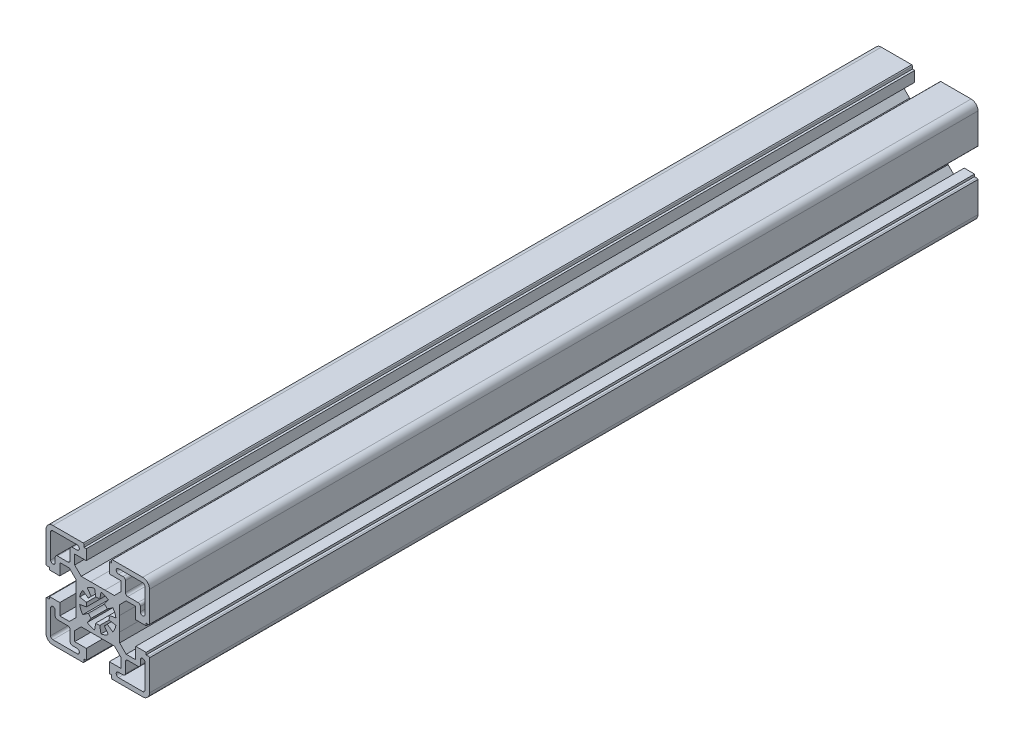
SolidWorks part; units mm, degrees
material "7050-T73510"
ref_plane "Front Plane" through (0, 0, 0) normal (0, 0, 1) x (1, 0, 0)
ref_plane "Top Plane" through (0, 0, 0) normal (0, 1, 0) x (1, 0, 0)
ref_plane "Right Plane" through (0, 0, 0) normal (1, 0, 0) x (0, 0, -1)
sketch "Sketch1" plane through (0, 0, 0) normal (0, 0, 1) x (1, 0, 0)
  line L0 (0, 34.901) -> (0, -38.8683) construction
  line L1 (-27.7848, -31.1091) -> (42.6814, -31.1091) construction
  line L3 (-0.8682, 4.924) -> (-1.3892, 7.8785)
  line L4 (-4.5886, 6.5532) -> (-2.8679, 4.0957)
  line L5 (-4.0957, 2.8679) -> (-6.5532, 4.5886)
  line L6 (-7.8784, 1.3892) -> (-4.924, 0.8682)
  line L10 (4.924, 0.8682) -> (7.8785, 1.3892)
  line L12 (6.5532, 4.5886) -> (4.0957, 2.8679)
  line L30 (-9.5, 3.1227) -> (-9.5, 7.207)
  line L31 (-9.5, 7.207) -> (-12.3429, 10.0499)
  line L32 (-12.3429, 10.0499) -> (-16.5, 10.0499)
  line L33 (-16.5, 10.0499) -> (-16.5, 4.9999)
  line L34 (-16.5, 4.9999) -> (-20.9999, 4.9999)
  line L35 (-20.9999, 4.9999) -> (-20.9999, 6)
  line L36 (-20.9999, 6) -> (-21.9999, 6)
  line L37 (-22.4999, 6.2999) -> (-22.4999, 19.5)
  line L38 (-19.4999, 22.5) -> (-6.3, 22.5)
  line L39 (-6, 21.9999) -> (-6, 20.9999)
  line L40 (-6, 20.9999) -> (-5, 20.9999)
  line L41 (-5, 20.9999) -> (-5, 16.5)
  line L42 (-5, 16.5) -> (-10.0501, 16.5)
  line L43 (-10.0501, 16.5) -> (-10.0501, 12.3428)
  line L44 (-10.0501, 12.3428) -> (-7.2071, 9.4999)
  line L45 (-7.2071, 9.4999) -> (-3.1228, 9.4999)
  line L82 (2.8679, 4.0957) -> (4.5886, 6.5532)
  line L83 (1.3892, 7.8784) -> (0.8682, 4.924)
  line L85 (3.1227, 9.5) -> (7.207, 9.5)
  line L86 (7.207, 9.5) -> (10.0499, 12.3429)
  line L87 (10.0499, 12.3429) -> (10.0499, 16.5)
  line L94 (-17.5001, 12) -> (-13.0001, 12)
  line L95 (-12.0001, 13) -> (-12.0001, 17.4999)
  line L96 (-11.0001, 18.4999) -> (-9.0001, 18.4999)
  line L97 (-19.5001, 20.5) -> (-9.0001, 20.5)
  line L98 (-20.5001, 8.9999) -> (-20.5001, 19.5)
  line L99 (-18.5001, 8.9999) -> (-18.5001, 11)
  line L101 (10.0499, 16.5) -> (4.9999, 16.5)
  line L102 (4.9999, 16.5) -> (4.9999, 20.9999)
  line L103 (4.9999, 20.9999) -> (6, 20.9999)
  line L104 (6, 20.9999) -> (6, 21.9999)
  line L105 (6.2999, 22.4999) -> (19.5, 22.4999)
  line L110 (22.5, 19.4999) -> (22.5, 6.3)
  line L111 (21.9999, 6) -> (20.9999, 6)
  line L118 (-3.1228, 9.4999) -> (3.1227, 9.5)
  line L119 (20.9999, 6) -> (20.9999, 5)
  line L124 (20.9999, 5) -> (16.5, 5)
  line L125 (16.5, 5) -> (16.5, 10.0501)
  line L126 (16.5, 10.0501) -> (12.3428, 10.0501)
  line L127 (12.3428, 10.0501) -> (9.4999, 7.2071)
  line L128 (9.4999, 7.2071) -> (9.4999, 3.1228)
  line L129 (12, 17.5001) -> (12, 13.0001)
  line L130 (13, 12.0001) -> (17.4999, 12.0001)
  line L131 (18.4999, 11.0001) -> (18.4999, 9.0001)
  line L132 (20.5, 19.5001) -> (20.5, 9.0001)
  line L133 (8.9999, 20.5001) -> (19.5, 20.5001)
  line L134 (8.9999, 18.5001) -> (11, 18.5001)
  line L135 (-9.5, 3.1227) -> (-9.4999, -3.1228)
  line L136 (9.4999, 3.1228) -> (9.5, -3.1227)
  line L137 (3.1228, -9.4999) -> (-3.1227, -9.5)
  line L138 (-0.8682, 4.924) -> (-1.3892, 7.8785)
  line L147 (0.8682, -4.924) -> (1.3892, -7.8785)
  line L148 (4.5886, -6.5532) -> (2.8679, -4.0957)
  line L149 (-4.924, -0.8682) -> (-7.8785, -1.3892)
  line L154 (4.0957, -2.8679) -> (6.5532, -4.5886)
  line L155 (7.8784, -1.3892) -> (4.924, -0.8682)
  line L157 (9.5, -3.1227) -> (9.5, -7.207)
  line L158 (9.5, -7.207) -> (12.3429, -10.0499)
  line L159 (12.3429, -10.0499) -> (16.5, -10.0499)
  line L160 (16.5, -10.0499) -> (16.5, -4.9999)
  line L161 (16.5, -4.9999) -> (20.9999, -4.9999)
  line L162 (20.9999, -4.9999) -> (20.9999, -6)
  line L163 (20.9999, -6) -> (21.9999, -6)
  line L164 (22.4999, -6.2999) -> (22.4999, -19.5)
  line L165 (19.4999, -22.5) -> (6.3, -22.5)
  line L166 (6, -21.9999) -> (6, -20.9999)
  line L167 (6, -20.9999) -> (5, -20.9999)
  line L168 (5, -20.9999) -> (5, -16.5)
  line L169 (5, -16.5) -> (10.0501, -16.5)
  line L176 (10.0501, -16.5) -> (10.0501, -12.3428)
  line L178 (4.924, 0.8682) -> (7.8785, 1.3892) [skipped]
  line L179 (6.5532, 4.5886) -> (4.0957, 2.8679) [skipped]
  line L180 (2.8679, 4.0957) -> (4.5886, 6.5532) [skipped]
  line L181 (1.3892, 7.8784) -> (0.8682, 4.924) [skipped]
  line L183 (3.1227, 9.5) -> (7.207, 9.5) [skipped]
  line L184 (7.207, 9.5) -> (10.0499, 12.3429) [skipped]
  line L185 (10.0499, 12.3429) -> (10.0499, 16.5) [skipped]
  line L186 (10.0499, 16.5) -> (4.9999, 16.5) [skipped]
  line L187 (4.9999, 16.5) -> (4.9999, 20.9999) [skipped]
  line L188 (4.9999, 20.9999) -> (6, 20.9999) [skipped]
  line L189 (6, 20.9999) -> (6, 21.9999) [skipped]
  line L190 (6.2999, 22.4999) -> (19.5, 22.4999) [skipped]
  line L191 (22.5, 19.4999) -> (22.5, 6.3) [skipped]
  line L192 (21.9999, 6) -> (20.9999, 6) [skipped]
  line L193 (20.9999, 6) -> (20.9999, 5) [skipped]
  line L194 (20.9999, 5) -> (16.5, 5) [skipped]
  line L195 (16.5, 5) -> (16.5, 10.0501) [skipped]
  line L196 (16.5, 10.0501) -> (12.3428, 10.0501) [skipped]
  line L197 (12.3428, 10.0501) -> (9.4999, 7.2071) [skipped]
  line L198 (9.4999, 7.2071) -> (9.4999, 3.1228) [skipped]
  line L199 (12, 17.5001) -> (12, 13.0001) [skipped]
  line L200 (13, 12.0001) -> (17.4999, 12.0001) [skipped]
  line L201 (18.4999, 11.0001) -> (18.4999, 9.0001) [skipped]
  line L202 (20.5, 19.5001) -> (20.5, 9.0001) [skipped]
  line L203 (8.9999, 20.5001) -> (19.5, 20.5001) [skipped]
  line L204 (8.9999, 18.5001) -> (11, 18.5001) [skipped]
  line L206 (0.8682, -4.924) -> (1.3892, -7.8785) [skipped]
  line L207 (4.5886, -6.5532) -> (2.8679, -4.0957) [skipped]
  line L208 (4.0957, -2.8679) -> (6.5532, -4.5886) [skipped]
  line L209 (7.8784, -1.3892) -> (4.924, -0.8682) [skipped]
  line L210 (9.5, -3.1227) -> (9.5, -7.207) [skipped]
  line L211 (9.5, -7.207) -> (12.3429, -10.0499) [skipped]
  line L212 (12.3429, -10.0499) -> (16.5, -10.0499) [skipped]
  line L213 (16.5, -10.0499) -> (16.5, -4.9999) [skipped]
  line L214 (16.5, -4.9999) -> (20.9999, -4.9999) [skipped]
  line L215 (20.9999, -4.9999) -> (20.9999, -6) [skipped]
  line L216 (20.9999, -6) -> (21.9999, -6) [skipped]
  line L217 (22.4999, -6.2999) -> (22.4999, -19.5) [skipped]
  line L218 (19.4999, -22.5) -> (6.3, -22.5) [skipped]
  line L219 (6, -21.9999) -> (6, -20.9999) [skipped]
  line L220 (6, -20.9999) -> (5, -20.9999) [skipped]
  line L221 (5, -20.9999) -> (5, -16.5) [skipped]
  line L222 (5, -16.5) -> (10.0501, -16.5) [skipped]
  line L223 (10.0501, -16.5) -> (10.0501, -12.3428) [skipped]
  line L224 (10.0501, -12.3428) -> (7.2071, -9.4999) [skipped]
  line L225 (7.2071, -9.4999) -> (3.1228, -9.4999) [skipped]
  line L226 (17.5001, -12) -> (13.0001, -12) [skipped]
  line L227 (12.0001, -13) -> (12.0001, -17.4999) [skipped]
  line L228 (11.0001, -18.4999) -> (9.0001, -18.4999) [skipped]
  line L229 (19.5001, -20.5) -> (9.0001, -20.5) [skipped]
  line L230 (20.5001, -8.9999) -> (20.5001, -19.5) [skipped]
  line L231 (18.5001, -8.9999) -> (18.5001, -11) [skipped]
  line L235 (-6.5532, -4.5886) -> (-4.0957, -2.8679) [skipped]
  line L236 (-2.8679, -4.0957) -> (-4.5886, -6.5532) [skipped]
  line L237 (-1.3892, -7.8784) -> (-0.8682, -4.924) [skipped]
  line L238 (-3.1227, -9.5) -> (-7.207, -9.5) [skipped]
  line L239 (-7.207, -9.5) -> (-10.0499, -12.3429) [skipped]
  line L240 (-10.0499, -12.3429) -> (-10.0499, -16.5) [skipped]
  line L241 (-10.0499, -16.5) -> (-4.9999, -16.5) [skipped]
  line L242 (-4.9999, -16.5) -> (-4.9999, -20.9999) [skipped]
  line L243 (-4.9999, -20.9999) -> (-6, -20.9999) [skipped]
  line L244 (-6, -20.9999) -> (-6, -21.9999) [skipped]
  line L245 (-6.2999, -22.4999) -> (-19.5, -22.4999) [skipped]
  line L246 (-22.5, -19.4999) -> (-22.5, -6.3) [skipped]
  line L247 (-21.9999, -6) -> (-20.9999, -6) [skipped]
  line L248 (-20.9999, -6) -> (-20.9999, -5) [skipped]
  line L249 (-20.9999, -5) -> (-16.5, -5) [skipped]
  line L250 (-16.5, -5) -> (-16.5, -10.0501) [skipped]
  line L251 (-16.5, -10.0501) -> (-12.3428, -10.0501) [skipped]
  line L252 (-12.3428, -10.0501) -> (-9.4999, -7.2071) [skipped]
  line L253 (-9.4999, -7.2071) -> (-9.4999, -3.1228) [skipped]
  line L254 (-12, -17.5001) -> (-12, -13.0001) [skipped]
  line L255 (-13, -12.0001) -> (-17.4999, -12.0001) [skipped]
  line L256 (-18.4999, -11.0001) -> (-18.4999, -9.0001) [skipped]
  line L257 (-20.5, -19.5001) -> (-20.5, -9.0001) [skipped]
  line L258 (-8.9999, -20.5001) -> (-19.5, -20.5001) [skipped]
  line L259 (-8.9999, -18.5001) -> (-11, -18.5001) [skipped]
  line L261 (10.0501, -12.3428) -> (7.2071, -9.4999)
  line L262 (7.2071, -9.4999) -> (3.1228, -9.4999)
  line L263 (17.5001, -12) -> (13.0001, -12)
  line L264 (12.0001, -13) -> (12.0001, -17.4999)
  line L265 (11.0001, -18.4999) -> (9.0001, -18.4999)
  line L266 (19.5001, -20.5) -> (9.0001, -20.5)
  line L267 (20.5001, -8.9999) -> (20.5001, -19.5)
  line L268 (18.5001, -8.9999) -> (18.5001, -11)
  line L272 (4.924, 0.8682) -> (7.8785, 1.3892)
  line L275 (-4.924, -0.8682) -> (-7.8785, -1.3892)
  line L276 (-6.5532, -4.5886) -> (-4.0957, -2.8679)
  line L277 (-2.8679, -4.0957) -> (-4.5886, -6.5532)
  line L278 (-1.3892, -7.8784) -> (-0.8682, -4.924)
  line L280 (-3.1227, -9.5) -> (-7.207, -9.5)
  line L281 (-7.207, -9.5) -> (-10.0499, -12.3429)
  line L282 (-10.0499, -12.3429) -> (-10.0499, -16.5)
  line L283 (-10.0499, -16.5) -> (-4.9999, -16.5)
  line L284 (-4.9999, -16.5) -> (-4.9999, -20.9999)
  line L285 (-4.9999, -20.9999) -> (-6, -20.9999)
  line L286 (-6, -20.9999) -> (-6, -21.9999)
  line L287 (-6.2999, -22.4999) -> (-19.5, -22.4999)
  line L288 (-22.5, -19.4999) -> (-22.5, -6.3)
  line L289 (-21.9999, -6) -> (-20.9999, -6)
  line L290 (-20.9999, -6) -> (-20.9999, -5)
  line L291 (-20.9999, -5) -> (-16.5, -5)
  line L292 (-16.5, -5) -> (-16.5, -10.0501)
  line L293 (-16.5, -10.0501) -> (-12.3428, -10.0501)
  line L294 (-12.3428, -10.0501) -> (-9.4999, -7.2071)
  line L295 (-9.4999, -7.2071) -> (-9.4999, -3.1228)
  line L296 (-12, -17.5001) -> (-12, -13.0001)
  line L297 (-13, -12.0001) -> (-17.4999, -12.0001)
  line L298 (-18.4999, -11.0001) -> (-18.4999, -9.0001)
  line L299 (-20.5, -19.5001) -> (-20.5, -9.0001)
  line L300 (-8.9999, -20.5001) -> (-19.5, -20.5001)
  line L301 (-8.9999, -18.5001) -> (-11, -18.5001)
  line L305 (0.8682, -4.924) -> (1.3892, -7.8785)
  arc A1 (-1.3892, 7.8785) -> (-4.5886, 6.5532) centre (0, 0) ccw
  arc A2 (-2.8679, 4.0957) -> (-4.0957, 2.8679) centre (0, 0) ccw
  arc A3 (-6.5532, 4.5886) -> (-7.8784, 1.3892) centre (0, 0) ccw
  arc A4 (-4.924, 0.8682) -> (-4.924, -0.8682) centre (0, 0) ccw
  arc A7 (0.8682, 4.924) -> (-0.8682, 4.924) centre (0, 0) ccw
  arc A8 (7.8785, 1.3892) -> (6.5532, 4.5886) centre (0, 0) ccw
  arc A20 (-22.4999, 6.2999) -> (-21.9999, 6) centre (-22.041, 6.4983) ccw
  arc A21 (-19.4999, 22.5) -> (-22.4999, 19.5) centre (-19.4999, 19.5) ccw
  arc A22 (-6, 21.9999) -> (-6.3, 22.5) centre (-6.4984, 22.041) ccw
  arc A32 (4.0957, 2.8679) -> (2.8679, 4.0957) centre (0, 0) ccw
  arc A33 (4.5886, 6.5532) -> (1.3892, 7.8784) centre (0, 0) ccw
  arc A44 (-17.5001, 12) -> (-18.5001, 11) centre (-17.5001, 11) ccw
  arc A45 (-13.0001, 12) -> (-12.0001, 13) centre (-13.0001, 13) ccw
  arc A46 (-11.0001, 18.4999) -> (-12.0001, 17.4999) centre (-11.0001, 17.4999) ccw
  arc A47 (-9.0001, 18.4999) -> (-9.0001, 20.5) centre (-9.0001, 19.5) ccw
  arc A48 (-19.5001, 20.5) -> (-20.5001, 19.5) centre (-19.5001, 19.5) ccw
  arc A49 (-20.5001, 8.9999) -> (-18.5001, 8.9999) centre (-19.5001, 8.9999) ccw
  arc A51 (0.8682, 4.924) -> (-0.8682, 4.924) centre (0, 0) ccw
  arc A52 (4.924, -0.8682) -> (4.924, 0.8682) centre (0, 0) ccw
  arc A53 (6.2999, 22.4999) -> (6, 21.9999) centre (6.4983, 22.041) ccw
  arc A60 (-7.8785, -1.3892) -> (-6.5532, -4.5886) centre (0, 0) ccw
  arc A64 (22.5, 19.4999) -> (19.5, 22.4999) centre (19.5, 19.4999) ccw
  arc A65 (21.9999, 6) -> (22.5, 6.3) centre (22.041, 6.4984) ccw
  arc A66 (12, 17.5001) -> (11, 18.5001) centre (11, 17.5001) ccw
  arc A73 (7.8785, 1.3892) -> (6.5532, 4.5886) centre (0, 0) ccw [skipped]
  arc A74 (4.0957, 2.8679) -> (2.8679, 4.0957) centre (0, 0) ccw [skipped]
  arc A75 (4.5886, 6.5532) -> (1.3892, 7.8784) centre (0, 0) ccw [skipped]
  arc A76 (6.2999, 22.4999) -> (6, 21.9999) centre (6.4983, 22.041) ccw [skipped]
  arc A77 (22.5, 19.4999) -> (19.5, 22.4999) centre (19.5, 19.4999) ccw [skipped]
  arc A78 (21.9999, 6) -> (22.5, 6.3) centre (22.041, 6.4984) ccw [skipped]
  arc A79 (12, 17.5001) -> (11, 18.5001) centre (11, 17.5001) ccw [skipped]
  arc A80 (12, 13.0001) -> (13, 12.0001) centre (13, 13.0001) ccw [skipped]
  arc A81 (18.4999, 11.0001) -> (17.4999, 12.0001) centre (17.4999, 11.0001) ccw [skipped]
  arc A82 (18.4999, 9.0001) -> (20.5, 9.0001) centre (19.5, 9.0001) ccw [skipped]
  arc A83 (20.5, 19.5001) -> (19.5, 20.5001) centre (19.5, 19.5001) ccw [skipped]
  arc A84 (8.9999, 20.5001) -> (8.9999, 18.5001) centre (8.9999, 19.5001) ccw [skipped]
  arc A85 (1.3892, -7.8785) -> (4.5886, -6.5532) centre (0, 0) ccw [skipped]
  arc A86 (2.8679, -4.0957) -> (4.0957, -2.8679) centre (0, 0) ccw [skipped]
  arc A87 (6.5532, -4.5886) -> (7.8784, -1.3892) centre (0, 0) ccw [skipped]
  arc A88 (4.924, -0.8682) -> (4.924, 0.8682) centre (0, 0) ccw [skipped]
  arc A89 (22.4999, -6.2999) -> (21.9999, -6) centre (22.041, -6.4983) ccw [skipped]
  arc A90 (19.4999, -22.5) -> (22.4999, -19.5) centre (19.4999, -19.5) ccw [skipped]
  arc A91 (6, -21.9999) -> (6.3, -22.5) centre (6.4984, -22.041) ccw [skipped]
  arc A92 (17.5001, -12) -> (18.5001, -11) centre (17.5001, -11) ccw [skipped]
  arc A93 (13.0001, -12) -> (12.0001, -13) centre (13.0001, -13) ccw [skipped]
  arc A94 (11.0001, -18.4999) -> (12.0001, -17.4999) centre (11.0001, -17.4999) ccw [skipped]
  arc A95 (9.0001, -18.4999) -> (9.0001, -20.5) centre (9.0001, -19.5) ccw [skipped]
  arc A96 (19.5001, -20.5) -> (20.5001, -19.5) centre (19.5001, -19.5) ccw [skipped]
  arc A97 (20.5001, -8.9999) -> (18.5001, -8.9999) centre (19.5001, -8.9999) ccw [skipped]
  arc A98 (-4.0957, -2.8679) -> (-2.8679, -4.0957) centre (0, 0) ccw [skipped]
  arc A99 (-4.5886, -6.5532) -> (-1.3892, -7.8784) centre (0, 0) ccw [skipped]
  arc A100 (-0.8682, -4.924) -> (0.8682, -4.924) centre (0, 0) ccw [skipped]
  arc A101 (-6.2999, -22.4999) -> (-6, -21.9999) centre (-6.4983, -22.041) ccw [skipped]
  arc A102 (-22.5, -19.4999) -> (-19.5, -22.4999) centre (-19.5, -19.4999) ccw [skipped]
  arc A103 (-21.9999, -6) -> (-22.5, -6.3) centre (-22.041, -6.4984) ccw [skipped]
  arc A104 (-12, -17.5001) -> (-11, -18.5001) centre (-11, -17.5001) ccw [skipped]
  arc A105 (-12, -13.0001) -> (-13, -12.0001) centre (-13, -13.0001) ccw [skipped]
  arc A106 (-18.4999, -11.0001) -> (-17.4999, -12.0001) centre (-17.4999, -11.0001) ccw [skipped]
  arc A107 (-18.4999, -9.0001) -> (-20.5, -9.0001) centre (-19.5, -9.0001) ccw [skipped]
  arc A108 (-20.5, -19.5001) -> (-19.5, -20.5001) centre (-19.5, -19.5001) ccw [skipped]
  arc A109 (-8.9999, -20.5001) -> (-8.9999, -18.5001) centre (-8.9999, -19.5001) ccw [skipped]
  arc A110 (12, 13.0001) -> (13, 12.0001) centre (13, 13.0001) ccw
  arc A111 (18.4999, 11.0001) -> (17.4999, 12.0001) centre (17.4999, 11.0001) ccw
  arc A112 (18.4999, 9.0001) -> (20.5, 9.0001) centre (19.5, 9.0001) ccw
  arc A113 (20.5, 19.5001) -> (19.5, 20.5001) centre (19.5, 19.5001) ccw
  arc A114 (8.9999, 20.5001) -> (8.9999, 18.5001) centre (8.9999, 19.5001) ccw
  arc A115 (-1.3892, 7.8785) -> (-4.5886, 6.5532) centre (0, 0) ccw
  arc A116 (1.3892, -7.8785) -> (4.5886, -6.5532) centre (0, 0) ccw
  arc A117 (2.8679, -4.0957) -> (4.0957, -2.8679) centre (0, 0) ccw
  arc A118 (6.5532, -4.5886) -> (7.8784, -1.3892) centre (0, 0) ccw
  arc A119 (4.924, -0.8682) -> (4.924, 0.8682) centre (0, 0) ccw
  arc A120 (-0.8682, -4.924) -> (0.8682, -4.924) centre (0, 0) ccw
  arc A121 (22.4999, -6.2999) -> (21.9999, -6) centre (22.041, -6.4983) ccw
  arc A122 (19.4999, -22.5) -> (22.4999, -19.5) centre (19.4999, -19.5) ccw
  arc A123 (6, -21.9999) -> (6.3, -22.5) centre (6.4984, -22.041) ccw
  arc A124 (17.5001, -12) -> (18.5001, -11) centre (17.5001, -11) ccw
  arc A125 (13.0001, -12) -> (12.0001, -13) centre (13.0001, -13) ccw
  arc A126 (11.0001, -18.4999) -> (12.0001, -17.4999) centre (11.0001, -17.4999) ccw
  arc A127 (9.0001, -18.4999) -> (9.0001, -20.5) centre (9.0001, -19.5) ccw
  arc A128 (19.5001, -20.5) -> (20.5001, -19.5) centre (19.5001, -19.5) ccw
  arc A129 (20.5001, -8.9999) -> (18.5001, -8.9999) centre (19.5001, -8.9999) ccw
  arc A130 (7.8785, 1.3892) -> (6.5532, 4.5886) centre (0, 0) ccw
  arc A131 (-7.8785, -1.3892) -> (-6.5532, -4.5886) centre (0, 0) ccw
  arc A132 (-4.0957, -2.8679) -> (-2.8679, -4.0957) centre (0, 0) ccw
  arc A133 (-4.5886, -6.5532) -> (-1.3892, -7.8784) centre (0, 0) ccw
  arc A134 (-0.8682, -4.924) -> (0.8682, -4.924) centre (0, 0) ccw
  arc A135 (-4.924, 0.8682) -> (-4.924, -0.8682) centre (0, 0) ccw
  arc A136 (-6.2999, -22.4999) -> (-6, -21.9999) centre (-6.4983, -22.041) ccw
  arc A137 (-22.5, -19.4999) -> (-19.5, -22.4999) centre (-19.5, -19.4999) ccw
  arc A138 (-21.9999, -6) -> (-22.5, -6.3) centre (-22.041, -6.4984) ccw
  arc A139 (-12, -17.5001) -> (-11, -18.5001) centre (-11, -17.5001) ccw
  arc A140 (-12, -13.0001) -> (-13, -12.0001) centre (-13, -13.0001) ccw
  arc A141 (-18.4999, -11.0001) -> (-17.4999, -12.0001) centre (-17.4999, -11.0001) ccw
  arc A142 (-18.4999, -9.0001) -> (-20.5, -9.0001) centre (-19.5, -9.0001) ccw
  arc A143 (-20.5, -19.5001) -> (-19.5, -20.5001) centre (-19.5, -19.5001) ccw
  arc A144 (-8.9999, -20.5001) -> (-8.9999, -18.5001) centre (-8.9999, -19.5001) ccw
  arc A145 (1.3892, -7.8785) -> (4.5886, -6.5532) centre (0, 0) ccw
  point P528 (0, 0)
  dimension "D1" = 4
  dimension "D2" = 4
extrude "Boss-Extrude1" add sketch "Sketch1" along normal blind 360
